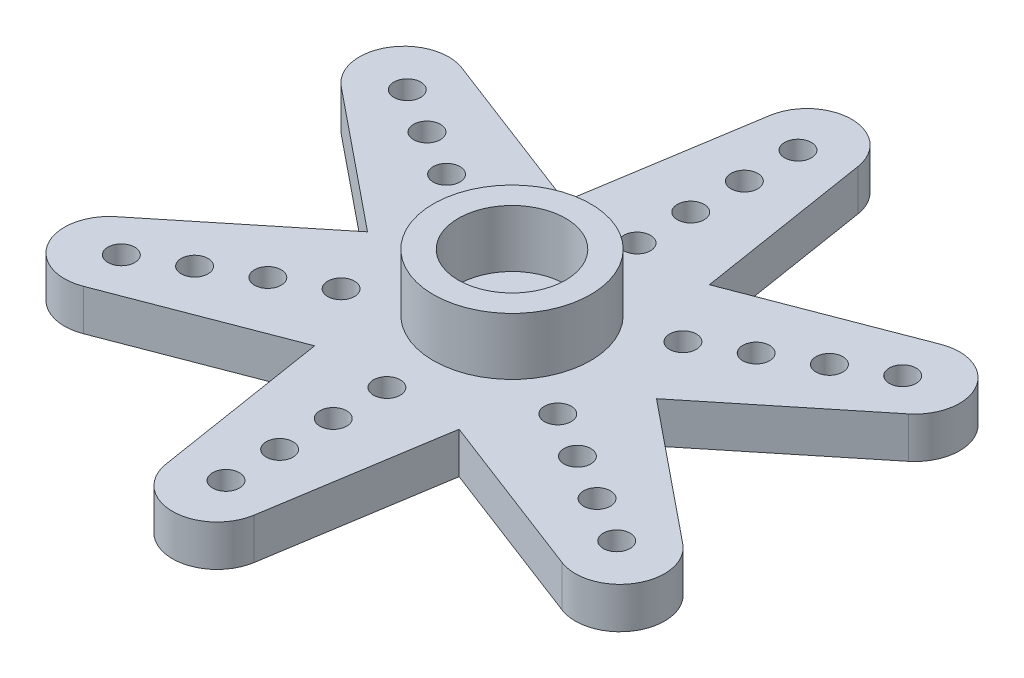
SolidWorks part; units mm, degrees
ref_plane "前视基准面" through (0, 0, 0) normal (0, 0, 1) x (1, 0, 0)
ref_plane "上视基准面" through (0, 0, 0) normal (0, 1, 0) x (1, 0, 0)
ref_plane "右视基准面" through (0, 0, 0) normal (1, 0, 0) x (0, 0, -1)
sketch "Sketch1" plane through (0, 0, 0) normal (0, 1, 0) x (1, 0, 0)
  circle A0 centre (0, 0) radius 6.1
  circle A1 centre (0, 0) radius 1.5
  dimension "D1" = 12.2
  dimension "D2" = 3
extrude "Boss-Extrude1" add sketch "Sketch1" along normal blind 2.3
sketch "Sketch2" plane through (0, 2.3, 0) normal (0, 1, 0) x (1, 0, 0)
  circle A0 centre (0, 0) radius 4.4
  circle A1 centre (0, 0) radius 3
  dimension "D1" = 8.8
  dimension "D2" = 6
extrude "Boss-Extrude2" add sketch "Sketch2" along normal blind 3.2
sketch "Sketch3" plane through (0, 0, 0) normal (0, -1, 0) x (1, 0, 0)
  line L0 (0, 0) -> (0, -19) construction
  line L1 (-2.469, -16.8925) -> (-4.5, -4.1183)
  line L2 (2.469, -16.8925) -> (4.5, -4.1183)
  arc A0 (-2.469, -16.8925) -> (2.469, -16.8925) centre (0, -16.5) ccw
  circle A1 centre (0, 0) radius 6.1 construction
  circle A2 centre (0, 0) radius 6.1
  circle A3 centre (0, -7) radius 0.75
  circle A4 centre (0, -10) radius 0.75
  circle A5 centre (0, -13) radius 0.75
  circle A6 centre (0, -16) radius 0.75
  circle A7 centre (0, 0) radius 1.5 construction
  point P12 (-6.1, 0)
  circle M3 centre (0, 0) radius 6.1
  dimension "D2" = 2.5
  dimension "D4" = 1.5
  dimension "D5" = 3
  dimension "D6" = 3
  dimension "D7" = 3
  dimension "D8" = 7
  dimension "D1" = 19
  dimension "D3" = 1.6
extrude "Boss-Extrude3" add sketch "Sketch3" against normal blind 2.3 contours A2 L0 A3 A4 A5 A6 A0 L2 | L0 L1 A0 A6 A5 A4 A3 M3
pattern_circular "CirPattern1" count 6 over 360 about axis through (0, 0, 0) along (0, 1, 0) of "Boss-Extrude3"
